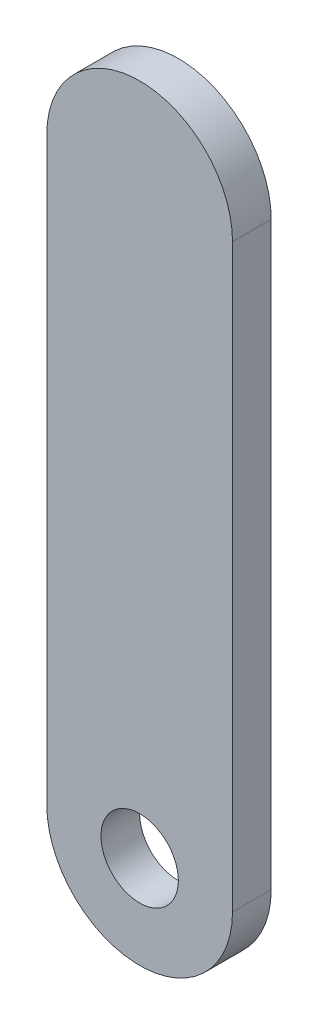
SolidWorks part; units mm, degrees
ref_plane "Plano frontal" through (0, 0, 0) normal (0, 0, 1) x (1, 0, 0)
ref_plane "Plano superior" through (0, 0, 0) normal (0, 1, 0) x (1, 0, 0)
ref_plane "Plano direito" through (0, 0, 0) normal (1, 0, 0) x (0, 0, -1)
sketch "Esboço1" plane through (0, 0, 0) normal (0, 0, 1) x (1, 0, 0)
  line L0 (0, 0) -> (0, 75) construction
  line L1 (-12, 0) -> (-12, 75)
  line L2 (12, 0) -> (12, 75)
  arc A0 (-12, 0) -> (12, 0) centre (0, 0) ccw
  arc A1 (12, 75) -> (-12, 75) centre (0, 75) ccw
  circle A2 centre (0, 0) radius 5
  point P3 (0, 37.5)
  dimension "D2" = 12
  dimension "D3" = 10
  dimension "D1" = 75
extrude "Ressalto-extrusão1" add sketch "Esboço1" along normal blind 5
